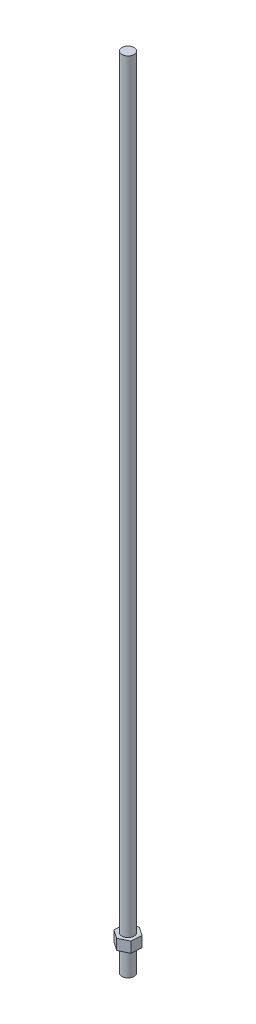
SolidWorks part; units mm, degrees
material "AISI 1010 Steel, hot rolled bar"
ref_plane "Front Plane" through (0, 0, 0) normal (0, 0, 1) x (1, 0, 0)
ref_plane "Top Plane" through (0, 0, 0) normal (0, 1, 0) x (1, 0, 0)
ref_plane "Right Plane" through (0, 0, 0) normal (1, 0, 0) x (0, 0, -1)
sketch "Sketch1" plane through (0, 0, 0) normal (0, 1, 0) x (1, 0, 0)
  circle A0 centre (0, 0) radius 6.35
  dimension "D1" = 12.7
extrude "Boss-Extrude1" add sketch "Sketch1" along normal blind 831.85
sketch "Sketch3" plane through (0, 0, 0) normal (0, 1, 0) x (1, 0, 0)
  line L1 (9.8769, 4.8389) -> (0.7478, 10.9731)
  line L2 (0.7478, 10.9731) -> (-9.129, 6.1342)
  line L3 (-9.129, 6.1342) -> (-9.8769, -4.8389)
  line L4 (-9.8769, -4.8389) -> (-0.7478, -10.9731)
  line L5 (-0.7478, -10.9731) -> (9.129, -6.1342)
  line L6 (9.129, -6.1342) -> (9.8769, 4.8389)
  circle A0 centre (0, 0) radius 9.525 construction
  dimension "D1" = 19.05
extrude "Boss-Extrude2" add sketch "Sketch3" along normal blind 11.049 from offset 25.4
